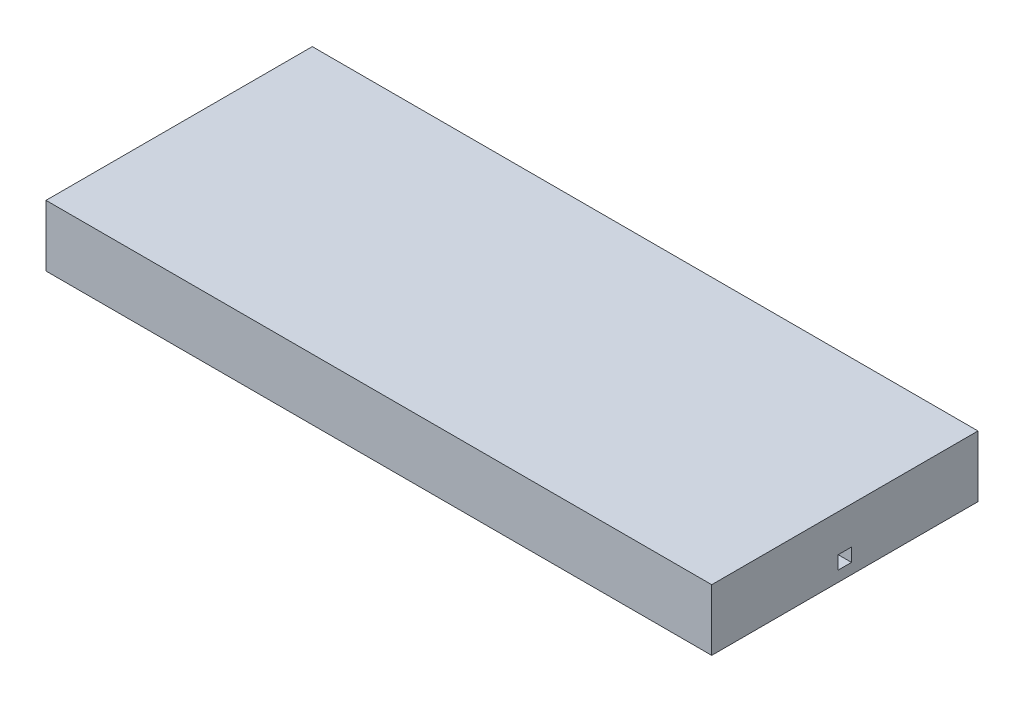
SolidWorks part; units mm, degrees
material "PDMS-MIT"
ref_plane "Front Plane" through (0, 0, 0) normal (0, 0, 1) x (1, 0, 0)
ref_plane "Top Plane" through (0, 0, 0) normal (0, 1, 0) x (1, 0, 0)
ref_plane "Right Plane" through (0, 0, 0) normal (1, 0, 0) x (0, 0, -1)
sketch "Sketch1" plane through (0, 0, 0) normal (0, 1, 0) x (1, 0, 0)
  line L1 (0, 0) -> (25, 0)
  line L2 (0, 0) -> (0, 10)
  line L3 (0, 10) -> (25, 10)
  line L4 (25, 0) -> (25, 10)
  dimension "D1" = 10
  dimension "D2" = 25
extrude "Boss-Extrude1" add sketch "Sketch1" along normal blind 2.3
sketch "Sketch2" plane through (0, 0, 0) normal (0, -1, 0) x (1, 0, 0)
  line L9 (8.625, -4.225) -> (7.775, -4.225)
  line L10 (8.625, -4.225) -> (8.625, -5.775)
  line L11 (8.625, -5.775) -> (7.775, -5.775)
  line L12 (7.775, -4.225) -> (7.775, -5.775)
  line L13 (8.625, -4.225) -> (7.775, -5.775) construction
  line L14 (8.625, -5.775) -> (7.775, -4.225) construction
  point P11 (8.2, -5)
  point P12 (8.2, -5)
  dimension "D8" = 0.85
  dimension "D9" = 1.55
extrude "Cut-Extrude1" cut sketch "Sketch2" against normal blind 0.4
sketch "Sketch3" plane through (0, 0, 0) normal (-1, 0, 0) x (0, 0, 1)
  line L0 (0, 2.3) -> (0, 0) construction
  line L1 (-4.75, 0.4) -> (-5.25, 0.4)
  line L2 (-4.75, 0.4) -> (-4.75, 0.9)
  line L3 (-4.75, 0.9) -> (-5.25, 0.9)
  line L4 (-5.25, 0.4) -> (-5.25, 0.9)
  line L5 (-4.75, 0.4) -> (-5.25, 0.9) construction
  line L6 (-4.75, 0.9) -> (-5.25, 0.4) construction
  line L7 (-10, 0) -> (0, 0) construction
  point P0 (-5, 0.65)
  dimension "D1" = 5
  dimension "Channelheight" = 0.5
  dimension "Channelwidth" = 0.5
  dimension "D2" = 0.4
extrude "Cut-Extrude2" cut sketch "Sketch3" against normal up to next
sketch "Sketch5" plane through (0, 0, 0) normal (0, -1, 0) x (1, 0, 0)
  line L0 (7.4029, -5.9739) -> (5.8327, -5.9739)
  line L1 (10.5885, -5.9967) -> (9.0184, -5.9967)
  line L2 (10.5885, -5.9967) -> (10.5885, -4.0852)
  line L3 (10.5885, -4.0852) -> (9.0184, -4.0852)
  line L4 (9.0184, -5.9967) -> (9.0184, -4.0852)
  line L5 (7.4029, -5.9739) -> (7.4029, -4.0624)
  line L6 (7.4029, -4.0624) -> (5.8327, -4.0624)
  line L7 (5.8327, -5.9739) -> (5.8327, -4.0624)
extrude "Cut-Extrude3" [suppressed] cut sketch "Sketch5" against normal blind 0.38
sketch "Sketch7" plane through (0, 0, 0) normal (0, -1, 0) x (1, 0, 0)
  line L0 (0, -10) -> (0, 0) construction
  line L9 (4.375, -6) -> (5.625, -6)
  line L10 (4.375, -6) -> (4.375, -4)
  line L11 (4.375, -4) -> (5.625, -4)
  line L12 (5.625, -6) -> (5.625, -4)
  line L13 (4.375, -6) -> (5.625, -4) construction
  line L14 (4.375, -4) -> (5.625, -6) construction
  line L15 (0, 0) -> (25, 0) construction
  line L16 (10.775, -6) -> (12.025, -6)
  line L17 (10.775, -6) -> (10.775, -4)
  line L18 (10.775, -4) -> (12.025, -4)
  line L19 (12.025, -6) -> (12.025, -4)
  line L20 (10.775, -6) -> (12.025, -4) construction
  line L21 (10.775, -4) -> (12.025, -6) construction
  point P3 (11.4, -5)
  point P4 (5, -5)
  dimension "D1" = 5
  dimension "D2" = 5
  dimension "D3" = 2
  dimension "D4" = 6.4
  dimension "SensorWidth" = 1.25
  dimension "SensorLength" = 2
sketch "Sketch6" [suppressed] plane through (25, 0, 0) normal (1, 0, 0) x (0, 0, -1)
  line L1 (0, 2.3) -> (10, 2.3)
  line L2 (0, 2.3) -> (0, 0)
  line L3 (0, 0) -> (10, 0)
  line L4 (10, 2.3) -> (10, 0)
  line L5 (4.6, 1.1) -> (5.4, 1.1)
  line L6 (4.6, 1.1) -> (4.6, 0.4)
  line L7 (4.6, 0.4) -> (5.4, 0.4)
  line L8 (5.4, 1.1) -> (5.4, 0.4)
extrude "Cut-Extrude4" cut sketch "Sketch7" against normal blind 0.4
extrude "Boss-Extrude2" [suppressed] add sketch "Sketch6" along normal blind 10
